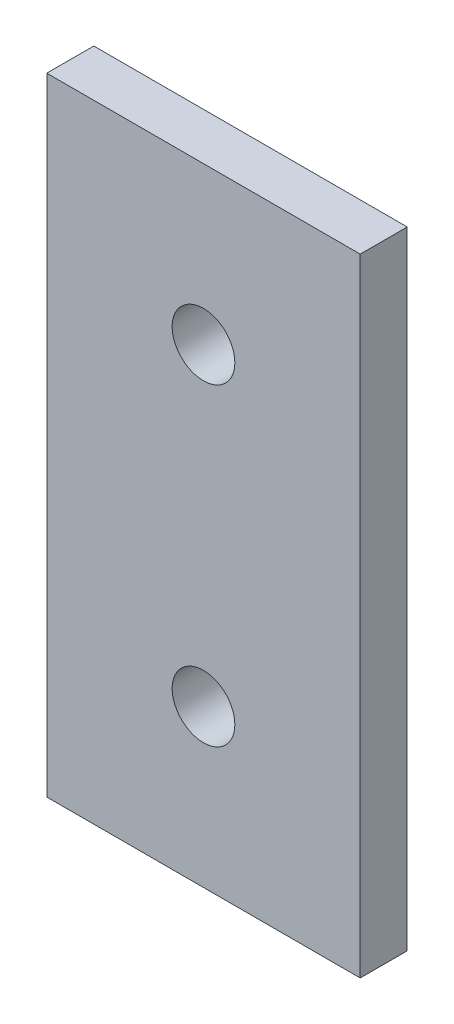
SolidWorks part; units mm, degrees
ref_plane "Front Plane" through (0, 0, 0) normal (0, 0, 1) x (1, 0, 0)
ref_plane "Top Plane" through (0, 0, 0) normal (0, 1, 0) x (1, 0, 0)
ref_plane "Right Plane" through (0, 0, 0) normal (1, 0, 0) x (0, 0, -1)
sketch "Sketch1" plane through (0, 0, 0) normal (0, 0, 1) x (1, 0, 0)
  line L1 (0, 0) -> (20, 0)
  line L2 (0, 0) -> (0, 40)
  line L3 (0, 40) -> (20, 40)
  line L4 (20, 0) -> (20, 40)
  dimension "D1" = 20
  dimension "D2" = 40
extrude "Boss-Extrude1" add sketch "Sketch1" along normal blind 3
sketch "Sketch2" plane through (0, 0, 3) normal (0, 0, 1) x (1, 0, 0)
  line L0 (0, 0) -> (20, 0) construction
  line L1 (20, 0) -> (20, 40) construction
  circle A0 centre (10, 10) radius 2
  dimension "D3" = 4
  dimension "D1" = 10
  dimension "D2" = 10
extrude "Cut-Extrude1" cut sketch "Sketch2" against normal through all
sketch "Sketch3" plane through (0, 0, 3) normal (0, 0, 1) x (1, 0, 0)
  line L0 (20, 0) -> (20, 40) construction
  line L1 (20, 40) -> (0, 40) construction
  circle A0 centre (10, 30) radius 2
  dimension "D1" = 4
  dimension "D2" = 10
  dimension "D3" = 10
extrude "Cut-Extrude2" cut sketch "Sketch3" against normal through all
